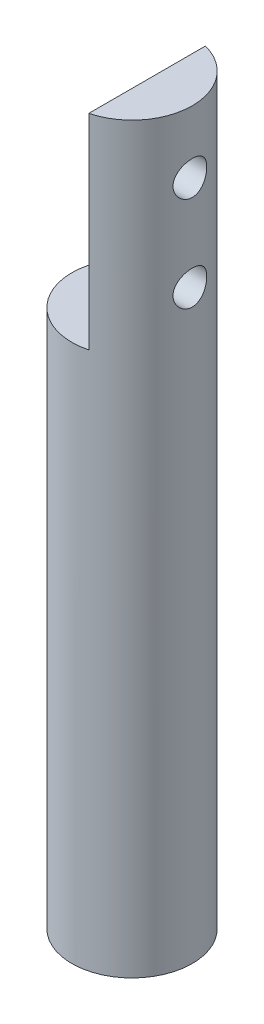
SolidWorks part; units mm, degrees
material "ABS"
ref_plane "Front" through (0, 0, 0) normal (0, 0, 1) x (1, 0, 0)
ref_plane "Top" through (0, 0, 0) normal (0, 1, 0) x (1, 0, 0)
ref_plane "Right" through (0, 0, 0) normal (1, 0, 0) x (0, 0, -1)
sketch "草图1" plane through (0, 0, 0) normal (0, 1, 0) x (1, 0, 0)
  circle A0 centre (0, 0) radius 3.175
extrude "凸台-拉伸1" add sketch "草图1" along normal blind 57.15
sketch "草图2" plane through (0, 57.15, 0) normal (0, 1, 0) x (1, 0, 0)
  line L0 (0, 0) -> (0, 3.175) construction
  line L1 (-0.794, 3.175) -> (0.794, 3.175)
  line L2 (0.794, 3.175) -> (0.794, -3.175)
  line L3 (0.794, -3.175) -> (-3.175, -3.175)
  line L4 (-3.175, -3.175) -> (-3.175, 3.175)
  line L5 (-3.175, 3.175) -> (-0.794, 3.175)
  line L6 (0, 0) -> (0.794, 0) construction
  circle A0 centre (0, 0) radius 3.175 construction
  point P8 (0, 3.175)
extrude "切除-拉伸1" cut sketch "草图2" against normal blind 10.795
sketch "草图3" plane through (0.794, 0, 0) normal (-1, 0, 0) x (0, 0, 1)
  line L0 (0, 57.15) -> (0, 53.855) construction
  line L1 (3.0741, 57.15) -> (-3.0741, 57.15) construction
  line L2 (0, 57.15) -> (0, 48.855) construction
  line L3 (0, 53.855) -> (0, 57.15) construction
  circle A0 centre (0, 53.855) radius 0.889
  circle A1 centre (0, 48.855) radius 0.889
extrude "切除-拉伸2" cut sketch "草图3" against normal blind 10.795
sketch "草图4" plane through (0, 0, 0) normal (0, -1, 0) x (1, 0, 0)
  line L0 (0, 0) -> (-3.175, 0) construction
  line L1 (-3.175, 0) -> (0, 0) construction
  line L2 (0, 0) -> (0, -3.175) construction
  line L3 (0, -3.175) -> (0, -1.5875) construction
  line L4 (0, -1.5875) -> (0, -2.3813) construction
  line L5 (0, -2.3813) -> (-1.9811, -2.3813) construction
  line L6 (-1.9811, -2.3813) -> (1.9451, -2.3813) construction
  line L7 (-1.9811, -2.3813) -> (1.9451, -2.3813)
  line L8 (1.9451, -2.3813) -> (1.9451, -3.175)
  line L9 (1.9451, -3.175) -> (-1.9811, -3.175)
  line L10 (-1.9811, -3.175) -> (-1.9811, -2.3813)
  circle A0 centre (0, 0) radius 3.175 construction
extrude "切除-拉伸3" cut sketch "草图4" against normal blind 8.573
sketch "草图5" plane through (0, 0, 0) normal (0, -1, 0) x (1, 0, 0)
  circle A0 centre (0, 0) radius 3.7749
extrude "切除-拉伸4" cut sketch "草图5" against normal blind 18
